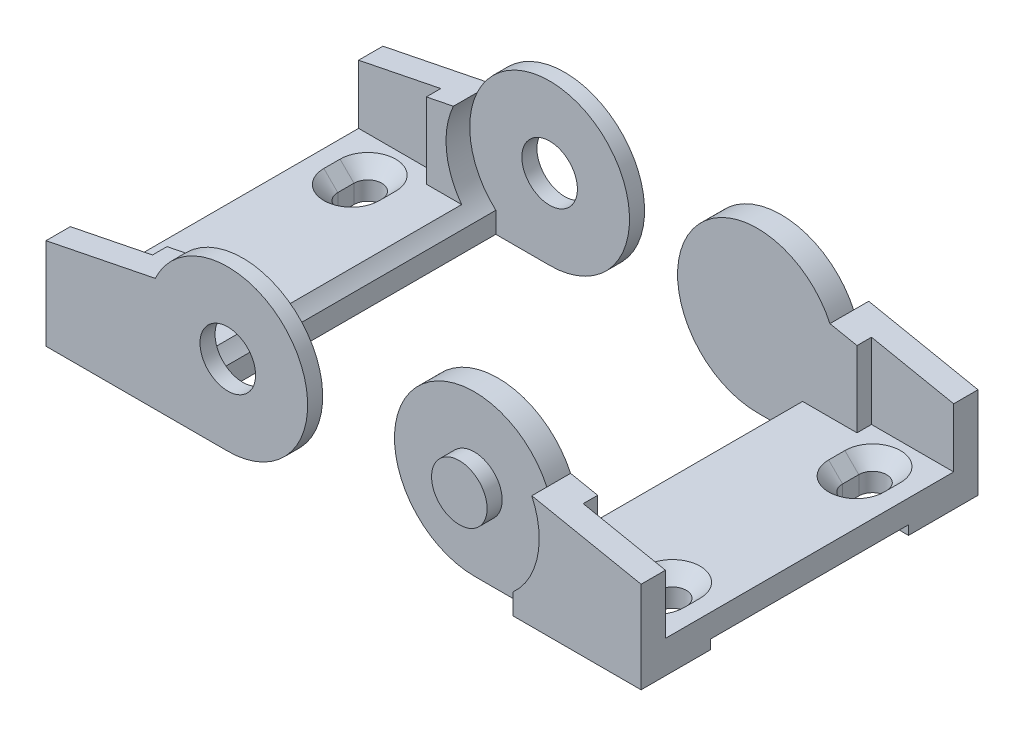
SolidWorks part; units mm, degrees
ref_plane "Front" through (0, 0, 0) normal (0, 0, 1) x (1, 0, 0)
ref_plane "Top" through (0, 0, 0) normal (0, 1, 0) x (1, 0, 0)
ref_plane "Right" through (0, 0, 0) normal (1, 0, 0) x (0, 0, -1)
sketch "Sketch1" plane through (0, 0, 0) normal (0, 0, 1) x (1, 0, 0)
  line L0 (0, -17.526) -> (39.878, -17.526)
  line L1 (39.878, -17.526) -> (39.878, 2.54)
  line L2 (39.878, 2.54) -> (15.9029, 7.366)
  line L3 (11.8049, -17.526) -> (11.8049, -12.954)
  arc A0 (11.8049, -12.954) -> (0, -17.526) centre (0, 0) ccw
  circle A1 centre (0, 0) radius 6.096
  dimension "D1" = 17.526
  dimension "D3" = 12.192
  dimension "D2" = 20.066
  dimension "D4" = 39.878
  dimension "D5" = 4.572
  dimension "D6" = 24.892
sketch "Sketch2" plane through (0, 0, 0) normal (0, 0, 1) x (1, 0, 0)
  line L0 (0, -17.526) -> (39.878, -17.526) construction
  line L1 (39.878, -17.526) -> (39.878, 2.54) construction
  line L2 (39.878, 2.54) -> (15.9029, 7.366) construction
  line L3 (0, -17.526) -> (39.878, -17.526)
  line L4 (39.878, -17.526) -> (39.878, 2.54)
  line L5 (39.878, 2.54) -> (15.9029, 7.366)
  arc A0 (11.8049, -12.954) -> (0, -17.526) centre (0, 0) ccw construction
  arc A1 (15.9029, 7.366) -> (0, -17.526) centre (0, 0) ccw
extrude "Extrude1" add sketch "Sketch2" along normal mid plane 73.914
sketch "Sketch3" plane through (0, 0, 0) normal (0, 0, 1) x (1, 0, 0)
  line L0 (39.878, -17.526) -> (39.878, 2.54) construction
  line L1 (39.878, 2.54) -> (15.9029, 7.366) construction
  line L2 (39.878, -10.414) -> (39.878, 2.54)
  line L3 (39.878, 2.54) -> (21.844, 6.1701)
  line L4 (21.844, -10.414) -> (39.878, -10.414)
  line L5 (21.844, 6.1701) -> (21.844, -10.414)
  dimension "D1" = 18.034
  dimension "D2" = 12.954
extrude "Cut-Extrude1" cut sketch "Sketch3" along normal offset from surface 5.334 and the other way offset from surface (31.623 mm away) 5.334 up to face at (18.2346, -2.6576, 36.957) other way up to face at (18.2346, -2.6576, -36.957)
sketch "Sketch4" plane through (0, 0, 0) normal (0, 0, 1) x (1, 0, 0)
  line L0 (21.844, -10.414) -> (39.878, -10.414) construction
  line L1 (9.906, -10.414) -> (39.878, -10.414)
  line L2 (9.906, -17.526) -> (9.906, -10.414)
  line L3 (0, -17.526) -> (39.878, -17.526)
  line L4 (39.878, -17.526) -> (39.878, 2.54)
  line L5 (39.878, 2.54) -> (15.9029, 7.366)
  line L6 (0, -17.526) -> (9.906, -17.526)
  line L7 (39.878, -10.414) -> (39.878, 2.54)
  line L8 (39.878, 2.54) -> (15.9029, 7.366)
  arc A1 (15.9029, 7.366) -> (0, -17.526) centre (0, 0) ccw
  arc A2 (15.9029, 7.366) -> (0, -17.526) centre (0, 0) ccw
  dimension "D2" = 29.972
  dimension "D1" = 0
extrude "Cut-Extrude2" cut sketch "Sketch4" against normal mid plane 56.896
sketch "Sketch5" plane through (0, 0, 36.957) normal (0, 0, 1) x (1, 0, 0)
  line L0 (0, -17.526) -> (39.878, -17.526) construction
  line L1 (11.8049, -17.526) -> (11.8049, -12.954) construction
  line L2 (0, -17.526) -> (11.8049, -17.526)
  line L3 (11.8049, -17.526) -> (11.8049, -12.954)
  circle A0 centre (0, 0) radius 6.096 construction
  arc A1 (11.8049, -12.954) -> (0, -17.526) centre (0, 0) ccw construction
  circle A2 centre (0, 0) radius 6.096
  arc A3 (11.8049, -12.954) -> (0, -17.526) centre (0, 0) ccw
extrude "Cut-Extrude3" cut sketch "Sketch5" against normal blind 3.302
sketch "Sketch6" plane through (0, -17.526, 0) normal (0, -1, 0) x (1, 0, 0)
  line L0 (39.878, 36.957) -> (39.878, -36.957) construction
  line L1 (33.782, -21.717) -> (39.878, -21.717)
  line L2 (33.782, -21.717) -> (33.782, 21.717)
  line L3 (33.782, 21.717) -> (39.878, 21.717)
  line L4 (39.878, -21.717) -> (39.878, 21.717)
  line L5 (0, 0) -> (39.878, 0) construction
  dimension "D1" = 6.096
  dimension "D2" = 43.434
extrude "Cut-Extrude4" cut sketch "Sketch6" against normal blind 2.032
sketch "Sketch7" plane through (0, -17.526, 0) normal (0, -1, 0) x (1, 0, 0)
  line L0 (26.924, 23.749) -> (26.924, 20.193)
  line L1 (33.02, 23.749) -> (33.02, 20.193)
  line L2 (39.878, 36.957) -> (39.878, 21.717) construction
  line L3 (0, 0) -> (48.2651, 0) construction
  line L4 (6.096, 0) -> (-6.096, 0) construction
  line L5 (26.924, 21.971) -> (33.02, 21.971) construction
  arc A0 (33.02, 23.749) -> (26.924, 23.749) centre (29.972, 23.749) ccw
  arc A1 (26.924, 20.193) -> (33.02, 20.193) centre (29.972, 20.193) ccw
  dimension "D1" = 3.048
  dimension "D2" = 3.556
  dimension "D3" = 9.906
  dimension "hole center" = 43.942
extrude "Cut-Extrude5" cut sketch "Sketch7" against normal blind 4.064
sketch "Sketch8" plane through (0, -13.462, 0) normal (0, -1, 0) x (1, 0, 0)
  line L2 (26.924, 23.749) -> (26.924, 20.193)
  line L3 (33.02, 20.193) -> (33.02, 23.749)
  line L4 (26.924, 23.749) -> (26.924, 20.193)
  line L5 (33.02, 20.193) -> (33.02, 23.749)
  arc A2 (33.02, 23.749) -> (26.924, 23.749) centre (29.972, 23.749) ccw
  arc A3 (26.924, 20.193) -> (33.02, 20.193) centre (29.972, 20.193) ccw
  arc A4 (33.02, 23.749) -> (26.924, 23.749) centre (29.972, 23.749) ccw
  arc A5 (26.924, 20.193) -> (33.02, 20.193) centre (29.972, 20.193) ccw
  dimension "D1" = 0
extrude "Cut-Extrude6" cut sketch "Sketch8" against normal up to surface (3.048 mm away) draft 45
mirror "Mirror1" about plane through (0, 0, 0) normal (0, 0, 1) of "Cut-Extrude3", "Cut-Extrude6", "Cut-Extrude5"
ref_plane "Plane1" through (-25.4, 0, 0) normal (1, 0, 0) x (0, 0, -1)
mirror "Mirror3" about plane through (-25.4, 0, 0) normal (1, 0, 0) of bodies 108
sketch "Sketch9" plane through (0, 0, 36.957) normal (0, 0, 1) x (1, 0, 0)
  circle A1 centre (-50.8, 0) radius 6.096
  circle A2 centre (-50.8, 0) radius 6.096
  dimension "D1" = 0
sketch "Sketch10" plane through (0, 0, 33.655) normal (0, 0, 1) x (1, 0, 0)
  line L2 (-62.6049, -12.954) -> (-62.6049, -17.526)
  line L3 (-62.6049, -17.526) -> (-50.8, -17.526)
  line L4 (-62.6049, -12.954) -> (-62.6049, -17.526)
  line L5 (-62.6049, -17.526) -> (-50.8, -17.526)
  arc A2 (-66.7029, 7.366) -> (-62.6049, -12.954) centre (-50.8, 0) ccw
  arc A3 (-50.8, -17.526) -> (-66.7029, 7.366) centre (-50.8, 0) ccw
  arc A4 (-66.7029, 7.366) -> (-62.6049, -12.954) centre (-50.8, 0) ccw
  arc A5 (-50.8, -17.526) -> (-66.7029, 7.366) centre (-50.8, 0) ccw
  dimension "D1" = 0
extrude "Extrude2" add sketch "Sketch10" along normal up to surface (3.302 mm away) up to face at (-75.319, -7.7542, 36.957)
sketch "Sketch11" plane through (0, 0, -33.655) normal (0, 0, -1) x (-1, 0, 0)
  line L2 (50.8, -17.526) -> (62.6049, -17.526)
  line L3 (62.6049, -17.526) -> (62.6049, -12.954)
  line L4 (50.8, -17.526) -> (62.6049, -17.526)
  line L5 (62.6049, -17.526) -> (62.6049, -12.954)
  arc A2 (62.6049, -12.954) -> (66.7029, 7.366) centre (50.8, 0) ccw
  arc A3 (66.7029, 7.366) -> (50.8, -17.526) centre (50.8, 0) ccw
  arc A4 (62.6049, -12.954) -> (66.7029, 7.366) centre (50.8, 0) ccw
  arc A5 (66.7029, 7.366) -> (50.8, -17.526) centre (50.8, 0) ccw
  dimension "D1" = 0
extrude "Extrude3" add sketch "Sketch11" along normal up to surface (3.302 mm away) up to face at (-75.319, -7.7542, -36.957)
sketch "Sketch12" plane through (0, 0, 0) normal (0, 0, 1) x (1, 0, 0)
  line L2 (-62.6049, -12.954) -> (-62.6049, -17.526)
  line L3 (-62.6049, -17.526) -> (-50.8, -17.526)
  line L4 (-62.6049, -12.954) -> (-62.6049, -17.526)
  line L5 (-62.6049, -17.526) -> (-50.8, -17.526)
  arc A2 (-50.8, -17.526) -> (-66.7029, 7.366) centre (-50.8, 0) ccw
  arc A3 (-66.7029, 7.366) -> (-62.6049, -12.954) centre (-50.8, 0) ccw
  arc A4 (-50.8, -17.526) -> (-66.7029, 7.366) centre (-50.8, 0) ccw
  arc A5 (-66.7029, 7.366) -> (-62.6049, -12.954) centre (-50.8, 0) ccw
  dimension "D1" = 0
extrude "Cut-Extrude7" cut sketch "Sketch12" along normal up to surface and the other way up to surface
extrude "Cut-Extrude8" cut sketch "Sketch9" against normal through all
sketch "Sketch13" plane through (0, 0, 0) normal (0, 1, 0) x (1, 0, 0)
  line L0 (-83.82, 20.193) -> (-83.82, 23.749) construction
  line L1 (-83.82, -20.193) -> (-83.82, -23.749) construction
  line L2 (33.02, -20.193) -> (33.02, -23.749) construction
  line L3 (33.02, 20.193) -> (33.02, 23.749) construction
  point P0 (-83.82, 21.971)
  point P1 (-83.82, -21.971)
  point P4 (33.02, -21.971)
  point P7 (33.02, 21.971)
  point P10 (-87.0253, 51.1436)
